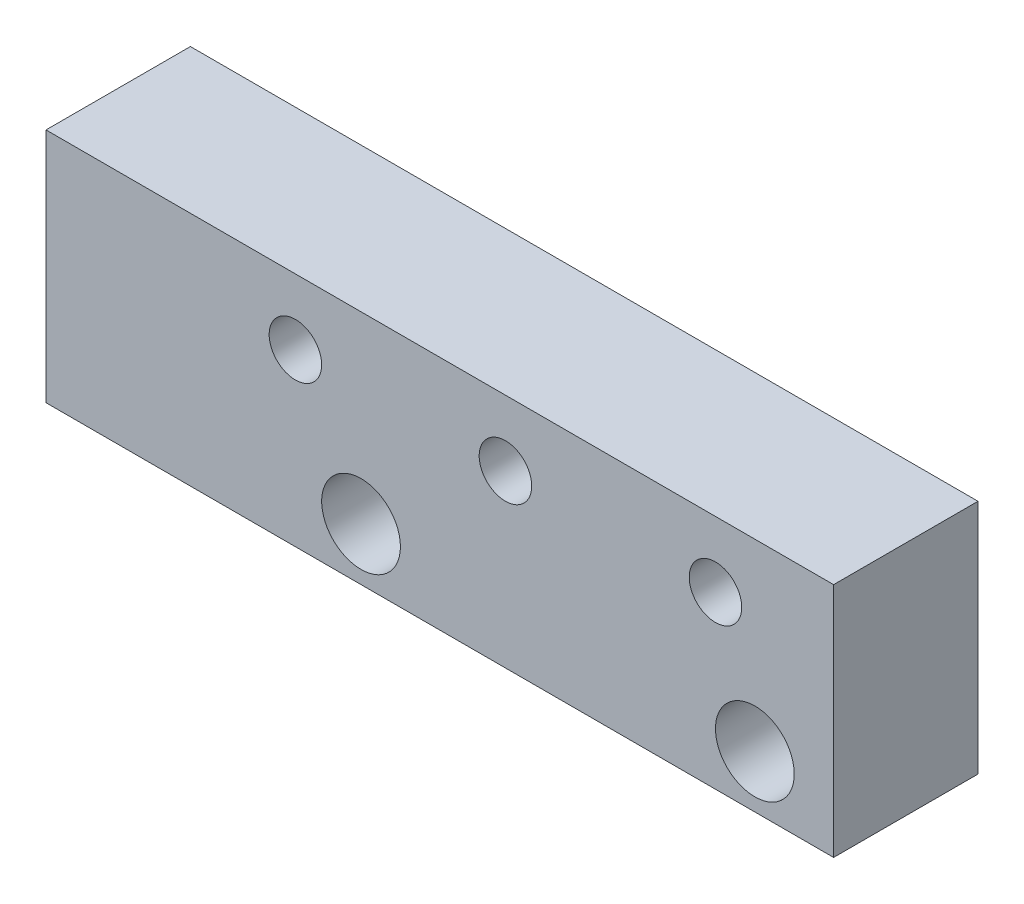
SolidWorks part; units mm, degrees
ref_plane "Plan de face" through (0, 0, 0) normal (0, 0, 1) x (1, 0, 0)
ref_plane "Plan de dessus" through (0, 0, 0) normal (0, 1, 0) x (1, 0, 0)
ref_plane "Plan de droite" through (0, 0, 0) normal (1, 0, 0) x (0, 0, -1)
sketch "Esquisse1" plane through (0, 0, 0) normal (0, 0, 1) x (1, 0, 0)
  line L1 (-19.1913, 2.8034) -> (10.8087, 2.8034)
  line L2 (-19.1913, 2.8034) -> (-19.1913, -6.1966)
  line L3 (-19.1913, -6.1966) -> (10.8087, -6.1966)
  line L4 (10.8087, 2.8034) -> (10.8087, -6.1966)
  dimension "D1" = 9
  dimension "D2" = 30
extrude "Boss.-Extru.1" add sketch "Esquisse1" along normal blind 5.5
sketch "Esquisse3" plane through (0, 0, 5.5) normal (0, 0, 1) x (1, 0, 0)
  line L1 (-19.1913, -6.1966) -> (10.8087, -6.1966) construction
  line L2 (10.8087, -6.1966) -> (10.8087, 2.8034) construction
  circle A0 centre (6.3087, 0.3034) radius 1
  circle A1 centre (-1.6913, 0.3034) radius 1
  circle A2 centre (-9.6913, 0.3034) radius 1
  dimension "D1" = 20.5
  dimension "D2" = 2
  dimension "D3" = 2
  dimension "D5" = 6.5
  dimension "D6" = 2
  dimension "D7" = 6.5
  dimension "D8" = 6.5
  dimension "D9" = 12.5
  dimension "D4" = 16
extrude "Enlèv. mat.-Extru.2" cut sketch "Esquisse3" against normal through all
sketch "Esquisse4" plane through (0, 0, 5.5) normal (0, 0, 1) x (1, 0, 0)
  line L0 (-19.1913, -6.1966) -> (10.8087, -6.1966) construction
  line L2 (10.8087, -6.1966) -> (10.8087, 2.8034) construction
  circle A0 centre (-7.1913, -4.1966) radius 1.5
  circle A1 centre (7.8087, -4.1966) radius 1.5
  dimension "D1" = 3
  dimension "D2" = 3
  dimension "D4" = 2
  dimension "D5" = 15
  dimension "D6" = 3
  dimension "D3" = 2
extrude "Enlèv. mat.-Extru.3" cut sketch "Esquisse4" against normal blind 10
